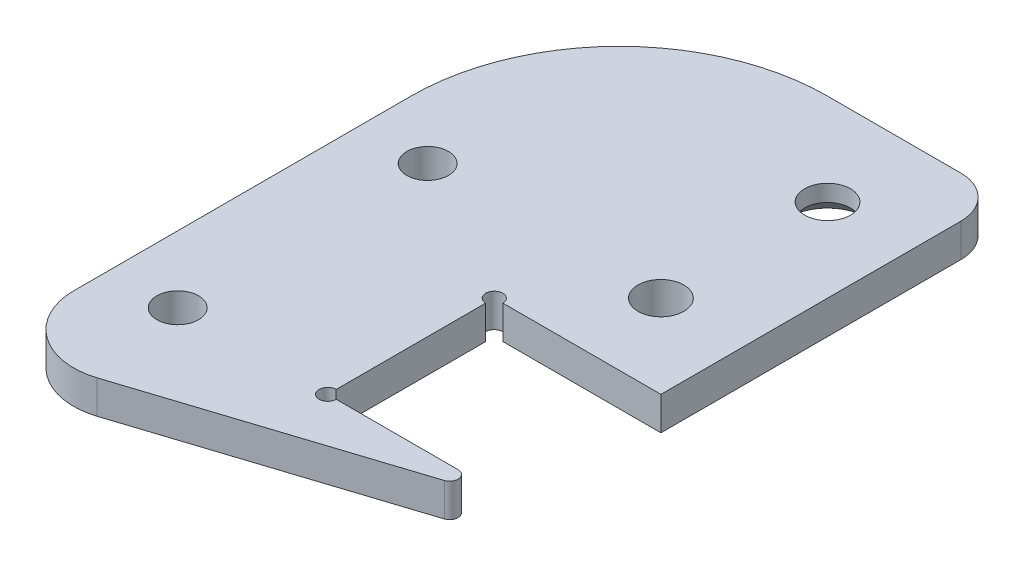
SolidWorks part; units mm, degrees
material "Thornel Mat VMA"
ref_plane "前视基准面" through (0, 0, 0) normal (0, 0, 1) x (1, 0, 0)
ref_plane "上视基准面" through (0, 0, 0) normal (0, 1, 0) x (1, 0, 0)
ref_plane "右视基准面" through (0, 0, 0) normal (1, 0, 0) x (0, 0, -1)
sketch "草图1" plane through (0, 0, 0) normal (0, 1, 0) x (1, 0, 0)
  line L0 (0, 0) -> (18, 0) construction
  line L1 (18, 0) -> (18, -14.5) construction
  line L2 (38, -4.5) -> (18, -4.5)
  line L3 (18, -4.5) -> (18, -24.5)
  line L4 (18, -24.5) -> (33.6441, -24.5)
  line L6 (33.9511, -26.4517) -> (2.4565, -36.6135)
  line L7 (-7.3921, -25.9412) -> (16.401, 31.5588) construction
  line L10 (18, -14.5) -> (60.4147, -14.5) construction
  line L11 (35, 21.5) -> (35, -0.5) construction
  line L12 (35, -0.5) -> (25, -0.5) construction
  line L13 (38, -4.5) -> (38, 31.5)
  line L15 (33, 36.5) -> (17, 36.5)
  line L16 (0, 0) -> (0, -29) construction
  line L18 (-8, 11.5) -> (-8, -29)
  arc A9 (2.4565, -36.6135) -> (-7.3921, -25.9412) centre (0, -29) cw construction
  arc A10 (33.6441, -24.5) -> (33.9511, -26.4517) centre (33.6441, -25.5) cw
  arc A18 (16.401, 31.5588) -> (23.7931, 36.5) centre (23.7931, 28.5) cw construction
  arc A19 (33, 36.5) -> (38, 31.5) centre (33, 31.5) cw
  arc A21 (-8, -29) -> (2.4565, -36.6135) centre (0, -29) ccw
  arc A22 (17, 36.5) -> (-8, 11.5) centre (17, 11.5) ccw
  circle A23 centre (28, 5.5) radius 2.75 construction
  circle A24 centre (28, 25.5) radius 2.75 construction
  circle A25 centre (28, 5.5) radius 2.75
  circle A26 centre (28, 25.5) radius 2.75
  circle A29 centre (0, 5.5) radius 2.5
  circle A30 centre (0, -24.5) radius 2.5
  point P5 (40.359, -5)
  point P13 (0, 0)
  point P17 (35, 10.5)
  point P37 (40, -24.5)
  dimension "D3" = 18
  dimension "D5" = 15
  dimension "D10" = 5
  dimension "D12" = 22
  dimension "D16" = 1
  dimension "D18" = 15
  dimension "D4" = 8
  dimension "D22" = 8
  dimension "D19" = 5
  dimension "D6" = 50
  dimension "D7" = 5
  dimension "D8" = 20
  dimension "D9" = 29
  dimension "D11" = 10
  dimension "D13" = 3
  dimension "D14" = 20
  dimension "D17" = 22
extrude "凸台-拉伸1" add sketch "草图1" along normal blind 4
chamfer "倒角1" [suppressed] distance 2 angle 45
chamfer "倒角2" distance 2 angle 45 1 edges at (28, 0, -22.75)
sketch "草图2" plane through (0, 4, 0) normal (0, 1, 0) x (1, 0, 0)
  circle A0 centre (18, -4.5) radius 1.025
  circle A1 centre (18, -24.5) radius 1.025
  dimension "D1" = 2.05
extrude "切除-拉伸1" cut sketch "草图2" against normal mid plane 10
